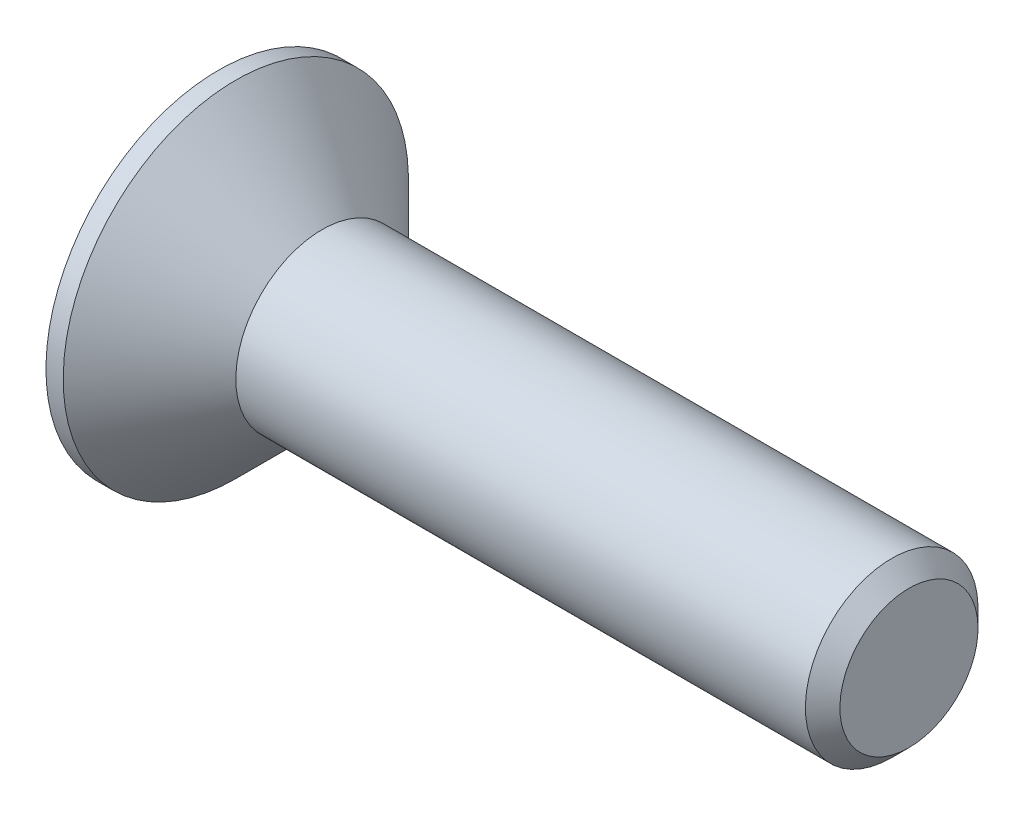
SolidWorks part; units mm, degrees
ref_plane "Front Plane" through (0, 0, 0) normal (0, 0, 1) x (1, 0, 0)
ref_plane "Top Plane" through (0, 0, 0) normal (0, 1, 0) x (1, 0, 0)
ref_plane "Right Plane" through (0, 0, 0) normal (1, 0, 0) x (0, 0, -1)
sketch "Sketch1" plane through (0, 0, 0) normal (0, 0, 1) x (1, 0, 0)
  line L0 (0, 1) -> (-1, 2)
  line L1 (-1, 2) -> (-1.2, 2)
  line L2 (-1.2, 2) -> (-1.2, 0)
  line L3 (-1.2, 0) -> (6.8, 0)
  line L4 (6.8, 0) -> (6.8, 1)
  line L5 (6.8, 1) -> (0, 1)
  dimension "D1" = 1
  dimension "D2" = 8
  dimension "D3" = 45
  dimension "D4" = 2
  dimension "D5" = 1.2
revolve "Revolve1" add sketch "Sketch1" angle 360 about L3
chamfer "Chamfer1" distance 0.2 angle 45 1 edges at (6.8, -1, 0)
sketch "Sketch2" plane through (-1.2, 0, 0) normal (-1, 0, 0) x (0, 0, 1)
  line L1 (-0.7506, 0) -> (-0.3753, -0.65)
  line L2 (-0.3753, -0.65) -> (0.3753, -0.65)
  line L3 (0.3753, -0.65) -> (0.7506, 0)
  line L4 (0.7506, 0) -> (0.3753, 0.65)
  line L5 (0.3753, 0.65) -> (-0.3753, 0.65)
  line L6 (-0.3753, 0.65) -> (-0.7506, 0)
  circle A0 centre (0, 0) radius 0.65 construction
  dimension "D1" = 1.3
extrude "Cut-Extrude1" cut sketch "Sketch2" against normal blind 0.75
